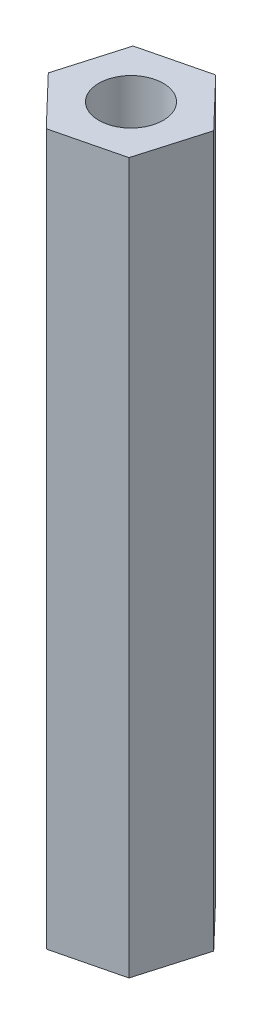
SolidWorks part; units mm, degrees
ref_plane "Front Plane" through (0, 0, 0) normal (0, 0, 1) x (1, 0, 0)
ref_plane "Top Plane" through (0, 0, 0) normal (0, 1, 0) x (1, 0, 0)
ref_plane "Right Plane" through (0, 0, 0) normal (1, 0, 0) x (0, 0, -1)
sketch "Sketch1" plane through (0, 0, 0) normal (0, 1, 0) x (1, 0, 0)
  line L1 (-2.7677, 3.3349) -> (-1.7448, 6.8555)
  line L2 (-1.7448, 6.8555) -> (-4.2822, 9.5017)
  line L3 (-4.2822, 9.5017) -> (-7.8426, 8.6273)
  line L4 (-7.8426, 8.6273) -> (-8.8655, 5.1067)
  line L5 (-8.8655, 5.1067) -> (-6.3281, 2.4605)
  line L6 (-6.3281, 2.4605) -> (-2.7677, 3.3349)
  circle A0 centre (-5.3052, 5.9811) radius 3.175 construction
  dimension "D1" = 6.35
extrude "Boss-Extrude1" add sketch "Sketch1" along normal blind 38.1
sketch "Sketch2" plane through (0, 38.1, 0) normal (0, 1, 0) x (1, 0, 0)
  line L0 (-7.8426, 8.6273) -> (-2.7677, 3.3349) construction
  circle A0 centre (-5.3052, 5.9811) radius 1.7272
  dimension "D1" = 3.4544
extrude "Cut-Extrude1" cut sketch "Sketch2" against normal blind 9.525
sketch "Sketch3" plane through (0, 0, 0) normal (0, -1, 0) x (1, 0, 0)
  line L0 (-4.2822, -9.5017) -> (-6.3281, -2.4605) construction
  circle A0 centre (-5.3052, -5.9811) radius 1.7272
  dimension "D1" = 3.4544
extrude "Cut-Extrude2" cut sketch "Sketch3" against normal blind 9.525
